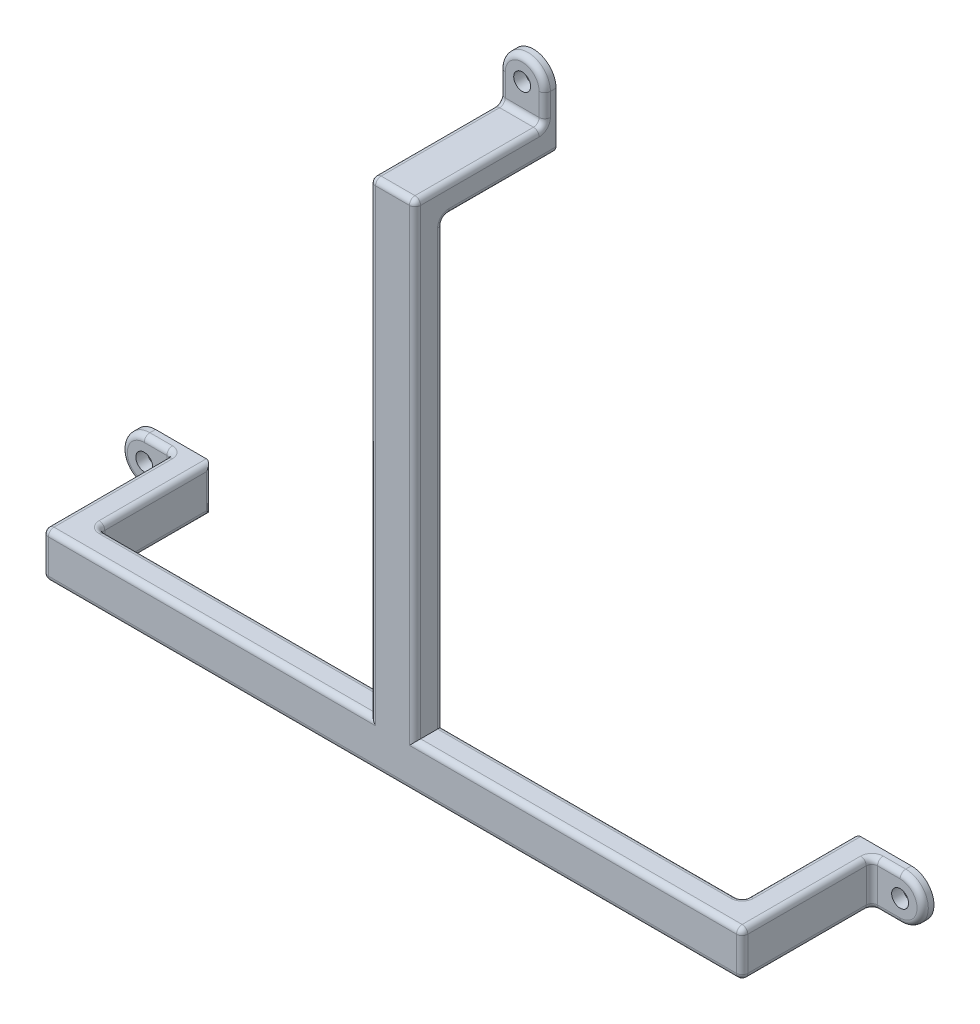
SolidWorks part; units mm, degrees
ref_plane "Front Plane" through (0, 0, 0) normal (0, 0, 1) x (1, 0, 0)
ref_plane "Top Plane" through (0, 0, 0) normal (0, 1, 0) x (1, 0, 0)
ref_plane "Right Plane" through (0, 0, 0) normal (1, 0, 0) x (0, 0, -1)
sketch "Sketch2" plane through (0, 0, 0) normal (0, 0, 1) x (1, 0, 0)
  line L0 (0, 0) -> (0, 91.9)
  line L1 (0, 0) -> (67, 0)
  line L2 (0, 0) -> (-67, 0)
  line L3 (4, 91.9) -> (4, 81.9)
  line L4 (4, 81.9) -> (-4, 81.9)
  line L5 (-4, 81.9) -> (-4, 91.9)
  line L6 (67, -4) -> (57, -4)
  line L7 (57, -4) -> (57, 4)
  line L8 (57, 4) -> (67, 4)
  line L9 (-67, 4) -> (-57, 4)
  line L10 (-57, 4) -> (-57, -4)
  line L11 (-57, -4) -> (-67, -4)
  arc A0 (4, 91.9) -> (-4, 91.9) centre (0, 91.9) ccw
  arc A1 (67, -4) -> (67, 4) centre (67, 0) ccw
  arc A2 (-67, 4) -> (-67, -4) centre (-67, 0) ccw
  circle A3 centre (0, 91.9) radius 1.5
  circle A4 centre (67, 0) radius 1.5
  circle A5 centre (-67, 0) radius 1.5
extrude "Boss-Extrude1" add sketch "Sketch2" along normal blind 2 contours L3 L4 L5 A0 | L9 L10 L11 A2 | L8 A1 L6 L7 | A3 | A4 | A5
sketch "Sketch3" plane through (0, 0, 2) normal (0, 0, 1) x (1, 0, 0)
  line L0 (4, 91.9) -> (4, 81.9) construction
  line L1 (-4, 81.9) -> (4, 81.9)
  line L2 (-4, 81.9) -> (-4, 86.9)
  line L3 (-4, 86.9) -> (4, 86.9)
  line L4 (4, 81.9) -> (4, 86.9)
  line L5 (-57, -4) -> (-67, -4) construction
  line L6 (-57, 4) -> (-62, 4)
  line L7 (-57, 4) -> (-57, -4)
  line L8 (-57, -4) -> (-62, -4)
  line L9 (-62, 4) -> (-62, -4)
  line L10 (67, -4) -> (57, -4) construction
  line L11 (57, 4) -> (62, 4)
  line L12 (57, 4) -> (57, -4)
  line L13 (57, -4) -> (62, -4)
  line L14 (62, 4) -> (62, -4)
  line M14 (-4, 91.9) -> (-4, 81.9)
  line M15 (-4, 81.9) -> (4, 81.9)
  line M16 (4, 81.9) -> (4, 91.9)
extrude "Boss-Extrude2" add sketch "Sketch3" along normal blind 23 contours L6 L9 L8 L7 | L3 M14 M15 M16 | L14 L11 L12 L13
sketch "Sketch4" plane through (57, 0, 0) normal (-1, 0, 0) x (0, 0, 1)
  line L0 (25, -4) -> (0, -4) construction
  line L1 (25, 4) -> (20, 4)
  line L2 (25, 4) -> (25, -4)
  line L3 (25, -4) -> (20, -4)
  line L4 (20, 4) -> (20, -4)
extrude "Boss-Extrude3" add sketch "Sketch4" along normal blind 115
sketch "Sketch5" plane through (0, 81.9, 0) normal (0, -1, 0) x (-1, 0, 0)
  line L0 (57, -20) -> (-57, -20) construction
  line L1 (4, -20) -> (-4, -20)
  line L2 (4, -20) -> (4, -25)
  line L3 (4, -25) -> (-4, -25)
  line L4 (-4, -20) -> (-4, -25)
  line L5 (4, -25) -> (4, 0) construction
  line L6 (-62, -25) -> (62, -25) construction
extrude "Boss-Extrude4" add sketch "Sketch5" along normal blind 85
fillet "Fillet1" radius 1 43 edges at (4, 89.4, 2) (-4, 89.4, 2) (0, 86.9, 2) (-4, 86.9, 13.5) (0, 86.9, 25) (4, 86.9, 13.5) (-4, 45.45, 25) (0, 95.9, 2) (0, 81.9, 0) (4, 81.9, 10) (-4, 81.9, 10) (0, 81.9, 20) (4, 42.95, 20) (-4, 42.95, 20) (4, 45.45, 25) (-57, 4, 10) (-64.5, 4, 2) (-57, 0, 20) (-57, -4, 10) (-71, 0, 2) (-57, 0, 0) (0, -4, 20) (57, -4, 10) (64.5, -4, 2) (0, -4, 25) (-62, -4, 13.5) (-64.5, -4, 2) (62, 4, 13.5) (64.5, 4, 2) (-62, 0, 2) (-62, 4, 13.5) (-33, 4, 25) (-62, 0, 25) (33, 4, 25) (30.5, 4, 20) (57, 0, 20) (-30.5, 4, 20) (57, 4, 10) (62, 0, 2) (71, 0, 2) (57, 0, 0) (62, 0, 25) (62, -4, 13.5)
